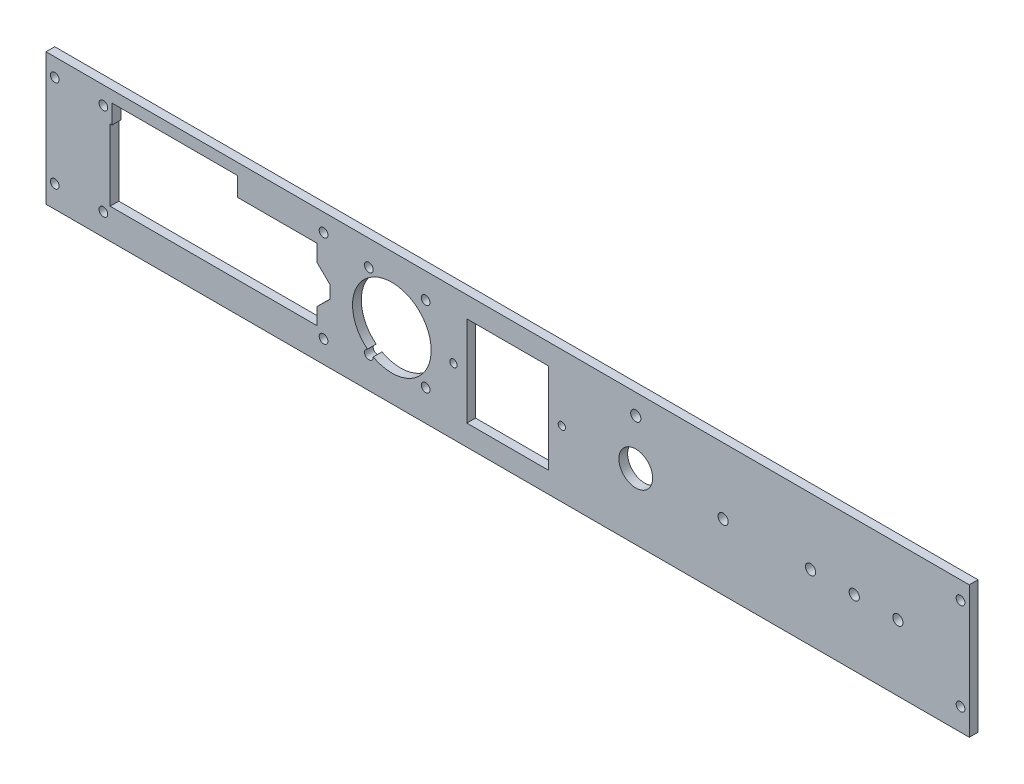
SolidWorks part; units mm, degrees
material "Acrylic (Medium-high impact)"
ref_plane "Front Plane" through (0, 0, 0) normal (0, 0, 1) x (1, 0, 0)
ref_plane "Top Plane" through (0, 0, 0) normal (0, 1, 0) x (1, 0, 0)
ref_plane "Right Plane" through (0, 0, 0) normal (1, 0, 0) x (0, 0, -1)
sketch "Sketch1" plane through (0, 0, 0) normal (0, 0, 1) x (1, 0, 0)
  line L1 (-161.5, 22.67) -> (161.5, 22.67)
  line L2 (-161.5, 22.67) -> (-161.5, -22.67)
  line L3 (-161.5, -22.67) -> (161.5, -22.67)
  line L4 (161.5, 22.67) -> (161.5, -22.67)
  line L5 (-161.5, 22.67) -> (161.5, -22.67) construction
  line L6 (-161.5, -22.67) -> (161.5, 22.67) construction
  point P0 (0, 0)
  dimension "D1" = 45.34
  dimension "D2" = 323
extrude "Boss-Extrude1" add sketch "Sketch1" along normal blind 3
sketch "Sketch2" plane through (0, 0, 3) normal (0, 0, 1) x (1, 0, 0)
  line L0 (-161.5, 22.67) -> (-161.5, -22.67) construction
  line L1 (-136.5, 12.25) -> (-65.5, 12.25)
  line L2 (-136.5, 12.25) -> (-136.5, -12.25)
  line L3 (-136.5, -12.25) -> (-65.5, -12.25)
  line L4 (-65.5, 12.25) -> (-65.5, -12.25)
  line L5 (-136.5, 12.25) -> (-65.5, -12.25) construction
  line L6 (-136.5, -12.25) -> (-65.5, 12.25) construction
  line L7 (161.5, 22.67) -> (-161.5, 22.67) construction
  line L8 (14, 0) -> (161.5, 0) construction
  line L9 (161.5, -22.67) -> (161.5, 22.67) construction
  line L10 (-136.5, 0) -> (-65.5, 0) construction
  line L11 (-14, 15.5) -> (14, 15.5)
  line L12 (-14, 15.5) -> (-14, -15.5)
  line L13 (-14, -15.5) -> (14, -15.5)
  line L14 (14, 15.5) -> (14, -15.5)
  line L15 (-14, 15.5) -> (14, -15.5) construction
  line L16 (-14, -15.5) -> (14, 15.5) construction
  line L21 (-65.5, 6.6) -> (-61, 2.2)
  line L22 (-61, 2.2) -> (-61, -2.2)
  line L23 (-61, -2.2) -> (-65.5, -6.6)
  line L24 (-65.5, -6.6) -> (-65.5, 6.6)
  circle A0 centre (-39.75, 0) radius 13.5
  circle A1 centre (44, 0) radius 5.8
  circle A2 centre (44, 15.67) radius 1.75
  circle A4 centre (74, 0) radius 1.75
  circle A5 centre (104, 0) radius 1.75
  circle A6 centre (119, 0) radius 1.75
  circle A7 centre (134, 0) radius 1.75
  point P0 (-101, 0)
  point P25 (0, 0)
  point P32 (-26.25, 0)
  point P34 (-14, 0)
  point P35 (-53.25, 0)
  point P36 (-61, 0)
  dimension "D4" = 27
  dimension "D6" = 11.6
  dimension "D7" = 3.5
  dimension "D8" = 30
  dimension "D10" = 3.5
  dimension "D11" = 147.5
  dimension "D12" = 30
  dimension "D16" = 87.5
  dimension "D23" = 3.5
  dimension "D24" = 3.5
  dimension "D25" = 3.5
  dimension "D1" = 24.5
  dimension "D2" = 71
  dimension "D3" = 25
  dimension "D5" = 12.25
  dimension "D9" = 7
  dimension "D13" = 28
  dimension "D14" = 31
  dimension "D15" = 39.75
  dimension "D17" = 4.5
  dimension "D18" = 4.4
  dimension "D19" = 13.2
  dimension "D20" = 12.25
  dimension "D21" = 12.25
  dimension "D22" = 30
  dimension "D27" = 15
  dimension "D28" = 15
extrude "Cut-Extrude1" cut sketch "Sketch2" against normal through all both contours L4 L1 L2 L3 | L23 L22 L21 L4 | A0 | L14 L11 L12 L13 | A1 | A2 | A4 | A5 | A6 | A7
sketch "Sketch3" plane through (0, 0, 0) normal (0, 0, -1) x (-1, 0, 0)
  line L0 (0, -22.67) -> (0, 22.67) construction
  line L5 (135.8, 18.75) -> (92.8, 18.75)
  line L6 (161.5, -22.67) -> (-161.5, -22.67) construction
  line L7 (-161.5, 22.67) -> (161.5, 22.67) construction
  line L8 (92.8, 18.75) -> (92.8, 11.75)
  line L9 (92.8, 11.75) -> (135.8, 11.75)
  line L10 (135.8, 11.75) -> (135.8, 18.75)
  line L11 (161.5, 22.67) -> (161.5, -22.67) construction
  circle A0 centre (63.2, 16.55) radius 1.5 construction
  circle A1 centre (63.2, 16.55) radius 1.5
  circle A2 centre (63.2, -15.05) radius 1.5 construction
  circle A3 centre (63.2, -15.05) radius 1.5
  circle A4 centre (138.8, -15.05) radius 1.5 construction
  circle A5 centre (138.8, 16.55) radius 1.5 construction
  circle A6 centre (138.8, -15.05) radius 1.5
  circle A7 centre (138.8, 16.55) radius 1.5
  circle A10 centre (155.5, 16.55) radius 1.5
  circle A11 centre (155.5, -15.05) radius 1.5
  circle A12 centre (-155.5, -15.05) radius 1.5
  circle A13 centre (-155.5, 16.55) radius 1.5
  point P18 (137.3, 16.55)
  point P27 (155.6454, -15.05)
  point P30 (0, 0)
  point P31 (155.5, 16.55)
  point P32 (0, 0)
  point P33 (155.5, -15.05)
  dimension "D5" = 3
  dimension "D6" = 6
  dimension "D8" = 3
  dimension "D1" = 1.5
  dimension "D2" = 7
  dimension "D3" = 43
  dimension "D4" = 2.2
  dimension "D7" = 6
extrude "Cut-Extrude2" cut sketch "Sketch3" against normal blind 10
sketch "Sketch5" plane through (0, 0, 3) normal (0, 0, 1) x (1, 0, 0)
  arc A0 (18.6, -1.25) -> (18.6, 1.25) centre (18.6, 0) ccw construction
  arc A1 (18.6, 1.25) -> (18.6, -1.25) centre (18.6, 0) ccw construction
  arc A2 (18.6, -1.25) -> (18.6, 1.25) centre (18.6, 0) ccw
  arc A3 (18.6, 1.25) -> (18.6, -1.25) centre (18.6, 0) ccw
  arc A4 (-18.6, -1.25) -> (-18.6, 1.25) centre (-18.6, 0) ccw construction
  arc A5 (-18.6, 1.25) -> (-18.6, -1.25) centre (-18.6, 0) ccw construction
  arc A6 (-18.6, -1.25) -> (-18.6, 1.25) centre (-18.6, 0) ccw
  arc A7 (-18.6, 1.25) -> (-18.6, -1.25) centre (-18.6, 0) ccw
extrude "Cut-Extrude4" cut sketch "Sketch5" against normal blind 10
sketch "Sketch6" plane through (0, 0, 3) normal (0, 0, 1) x (1, 0, 0)
  line L0 (-158.5, 22.67) -> (-158.5, -22.67)
  line L1 (161.5, 22.67) -> (-161.5, 22.67) construction
  line L2 (-161.5, -22.67) -> (161.5, -22.67) construction
  line L3 (-161.5, 22.67) -> (-161.5, -22.67) construction
  line L4 (158.5, 22.67) -> (158.5, -22.67)
  line L5 (161.5, -22.67) -> (161.5, 22.67) construction
  line L6 (158.5, 22.67) -> (161.5, 22.67)
  line L7 (161.5, 22.67) -> (161.5, -22.67)
  line L8 (161.5, -22.67) -> (158.5, -22.67)
  line L9 (-158.5, 22.67) -> (-161.5, 22.67)
  line L10 (-158.5, -22.67) -> (-161.5, -22.67)
  line L11 (-161.5, -22.67) -> (-161.5, 22.67)
  dimension "D1" = 3
  dimension "D2" = 3
extrude "Cut-Extrude5" cut sketch "Sketch6" against normal blind 10
sketch "Sketch7" plane through (0, 0, 0) normal (0, 0, -1) x (-1, 0, 0)
  circle A0 centre (28.15, -12) radius 1.5 construction
  circle A1 centre (47.65, -12) radius 1.5 construction
  circle A2 centre (28.15, -12) radius 1.5
  circle A3 centre (47.65, -12) radius 1.5
  circle A4 centre (47.65, 14) radius 1.5 construction
  circle A5 centre (28.15, 14) radius 1.5 construction
  circle A6 centre (47.65, 14) radius 1.5
  circle A7 centre (28.15, 14) radius 1.5
extrude "Cut-Extrude6" cut sketch "Sketch7" against normal through all
